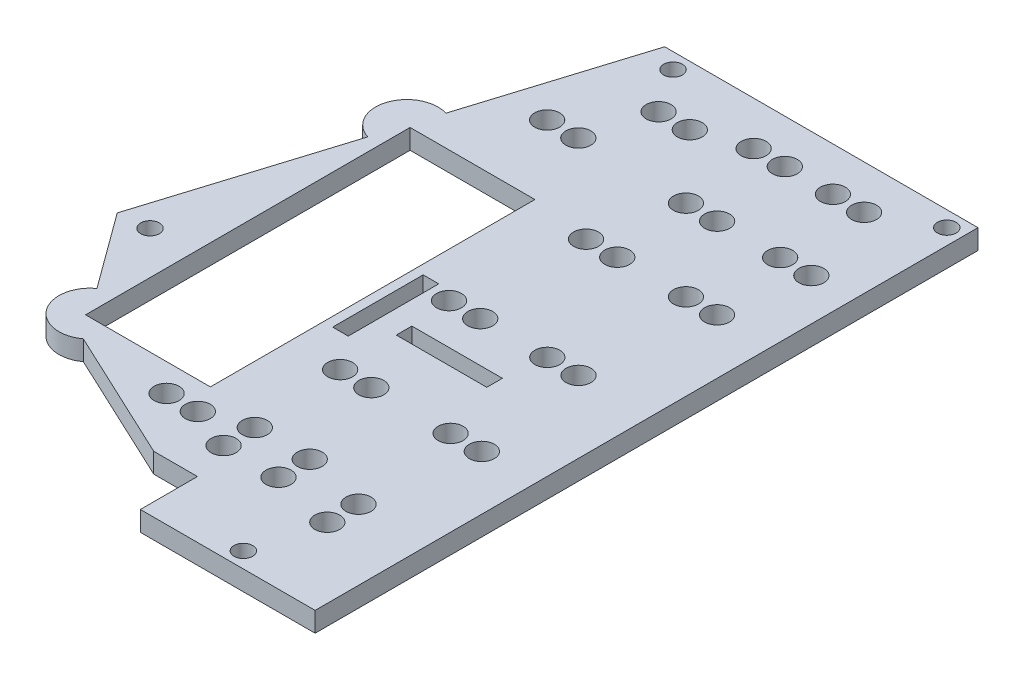
SolidWorks part; units mm, degrees
ref_plane "Front Plane" through (0, 0, 0) normal (0, 0, 1) x (1, 0, 0)
ref_plane "Top Plane" through (0, 0, 0) normal (0, 1, 0) x (1, 0, 0)
ref_plane "Right Plane" through (0, 0, 0) normal (1, 0, 0) x (0, 0, -1)
sketch "Sketch1" plane through (0, 0, 0) normal (0, 1, 0) x (1, 0, 0)
  line L0 (-22.0476, 28.7248) -> (28.1524, 28.7248)
  line L1 (28.1524, 28.7248) -> (28.1524, -68.2788)
  line L5 (28.1524, -68.2788) -> (28.1524, -38.2788) construction
  line L6 (-28.0953, -58.3719) -> (-6.8475, -68.3371)
  line L9 (-7.2476, -22.2752) -> (-9.7476, -22.2752)
  line L18 (-9.7476, -22.2752) -> (-9.7476, -36.7752)
  line L51 (-2.0476, -61.9488) -> (-8.7476, -61.9488) construction
  line L55 (-9.7476, -36.7752) -> (-7.2476, -36.7752)
  line L56 (-7.2476, -36.7752) -> (-7.2476, -22.2752)
  line L57 (10.9524, -30.2788) -> (10.9524, -32.7788)
  line L58 (-3.5476, -30.2788) -> (-3.5476, -32.7788)
  line L59 (-3.5476, -30.2788) -> (10.9524, -30.2788)
  line L60 (-3.5476, -32.7788) -> (10.9524, -32.7788)
  line L62 (-31.2476, -2.8652) -> (-11.2476, -2.8652)
  line L63 (-31.2476, -2.8652) -> (-31.2476, -54.8652)
  line L64 (-31.2476, -54.8652) -> (-11.2476, -54.8652)
  line L65 (-11.2476, -2.8652) -> (-11.2476, -54.8652)
  line L66 (-33.3284, -7.5653) -> (-42.8475, -38.1885)
  line L68 (-30.36, 1.9839) -> (-22.0476, 28.7248)
  line L70 (-42.8475, -38.1885) -> (-33.9913, -50.295)
  line L72 (28.1524, -68.2788) -> (28.1524, -77.4821)
  line L73 (28.1524, -77.4821) -> (0.1524, -77.4821)
  line L74 (-6.8475, -68.3371) -> (0.1524, -68.3371)
  line L75 (0.1524, -77.4821) -> (0.1524, -68.3371)
  circle A4 centre (25.6524, 26.2248) radius 1.5
  circle A7 centre (-38.0871, -37.6942) radius 1.5
  circle A8 centre (-18.207, 26.2212) radius 1.5
  circle A10 centre (16.9024, 21.7248) radius 2
  circle A11 centre (11.9024, 21.7248) radius 2
  circle A12 centre (4.2024, 21.7248) radius 2
  circle A13 centre (-0.7976, 21.7248) radius 2
  circle A14 centre (-8.5181, 19.2212) radius 2
  circle A15 centre (-13.5181, 19.2212) radius 2
  circle A16 centre (-16.3015, 9.1469) radius 2
  circle A17 centre (-21.3015, 9.1469) radius 2
  circle A18 centre (-2.0476, -61.9488) radius 2
  circle A19 centre (-2.0476, -56.9488) radius 2
  circle A20 centre (6.7524, -61.9488) radius 2
  circle A21 centre (6.7524, -56.9488) radius 2
  circle A22 centre (-8.8476, -59.2788) radius 2
  circle A23 centre (-13.8476, -59.2788) radius 2
  circle A24 centre (21.4524, 8.7248) radius 2
  circle A25 centre (16.4524, 8.7248) radius 2
  circle A26 centre (6.3524, 8.7248) radius 2
  circle A27 centre (1.3524, 8.7248) radius 2
  circle A28 centre (14.3524, -4.2752) radius 2
  circle A29 centre (19.3524, -4.2752) radius 2
  circle A30 centre (3.3524, -4.2752) radius 2
  circle A31 centre (-1.6476, -4.2752) radius 2
  circle A32 centre (16.6524, -23.7788) radius 2
  circle A33 centre (11.6524, -23.7788) radius 2
  circle A34 centre (0.9024, -23.7788) radius 2
  circle A35 centre (-4.0976, -23.7788) radius 2
  circle A36 centre (19.4524, -42.0752) radius 2
  circle A37 centre (14.4524, -42.0752) radius 2
  circle A38 centre (1.7524, -42.0752) radius 2
  circle A39 centre (-3.2476, -42.0752) radius 2
  circle A40 centre (16.9024, -59.2788) radius 2
  circle A41 centre (16.9024, -64.2788) radius 2
  arc A42 (-30.36, 1.9839) -> (-33.3284, -7.5653) centre (-31.8496, -2.789) ccw
  arc A43 (-33.9913, -50.295) -> (-28.0953, -58.3719) centre (-31.0457, -54.3352) ccw
  circle A44 centre (14.1524, -74.9821) radius 1.5
  point P38 (0, 0)
  dimension "D37" = 3
  dimension "D39" = 2.5
  dimension "D41" = 28
  dimension "D43" = 4
  dimension "D44" = 14
  dimension "D45" = 5
  dimension "D46" = 3
  dimension "D47" = 4
  dimension "D48" = 20
  dimension "D49" = 3
  dimension "D50" = 20
  dimension "D51" = 4
  dimension "D9" = 9.5037
  dimension "D13" = 4
  dimension "D15" = 4
  dimension "D19" = 4
  dimension "D21" = 4
  dimension "D26" = 4
  dimension "D28" = 4
  dimension "D29" = 4
  dimension "D30" = 4
  dimension "D32" = 17.2
  dimension "D52" = 4
  dimension "D53" = 4
  dimension "D56" = 4
  dimension "D58" = 4
  dimension "D60" = 4
  dimension "D36" = 21.4
  dimension "D23" = 4
  dimension "D66" = 4
  dimension "D70" = 4
  dimension "D74" = 4
  dimension "D75" = 4
  dimension "D78" = 4
  dimension "D81" = 4
  dimension "D84" = 4
  dimension "D90" = 8.7
  dimension "D101" = 5
  dimension "D102" = 5
  dimension "D4" = 30
  dimension "D5" = 71
  dimension "D6" = 25
  dimension "D7" = 35
  dimension "D10" = 6.7
  dimension "D11" = 11.25
  dimension "D12" = 7
  dimension "D14" = 5
  dimension "D16" = 7
  dimension "D17" = 7.7
  dimension "D18" = 7
  dimension "D20" = 5
  dimension "D22" = 7
  dimension "D24" = 5
  dimension "D25" = 5
  dimension "D27" = 70.8
  dimension "D31" = 5
  dimension "D33" = 2.5
  dimension "D34" = 35.4
  dimension "D35" = 51
  dimension "D38" = 2.5
  dimension "D55" = 8.8
  dimension "D57" = 8.8
  dimension "D61" = 5
  dimension "D62" = 21.4
  dimension "D63" = 37
  dimension "D64" = 10.1
  dimension "D65" = 20
  dimension "D67" = 5
  dimension "D68" = 20
  dimension "D69" = 8.8
  dimension "D71" = 33
  dimension "D72" = 33
  dimension "D73" = 5
  dimension "D76" = 11
  dimension "D77" = 33
  dimension "D79" = 5
  dimension "D80" = 33
  dimension "D82" = 11.5
  dimension "D85" = 5
  dimension "D87" = 5
  dimension "D89" = 10.75
  dimension "D91" = 5
  dimension "D92" = 12.7
  dimension "D93" = 5
  dimension "D94" = 5
  dimension "D96" = 11.25
  dimension "D97" = 52
  dimension "D98" = 20
  dimension "D99" = 39.4
  dimension "D100" = 31.59
extrude "Boss-Extrude1" add sketch "Sketch1" along normal blind 3.175
